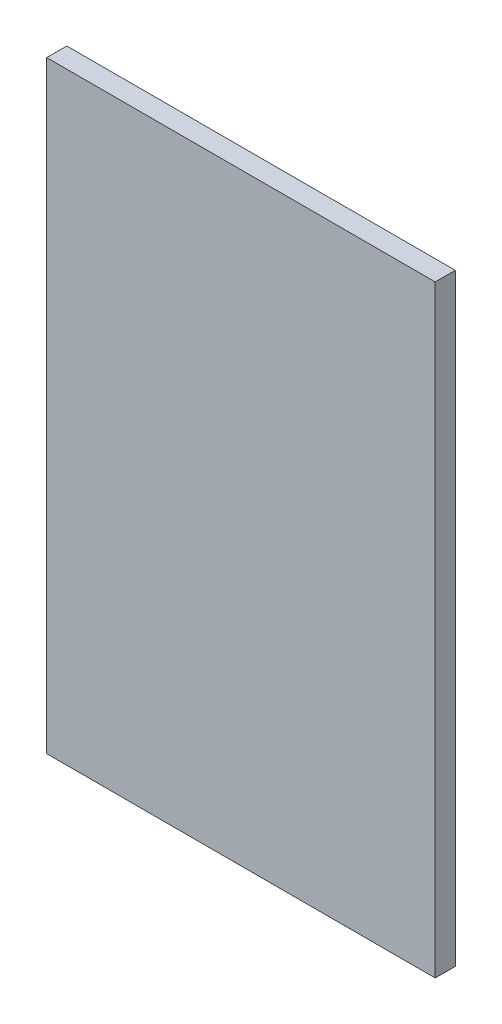
SolidWorks part; units mm, degrees
ref_plane "Plan de face" through (0, 0, 0) normal (0, 0, 1) x (1, 0, 0)
ref_plane "Plan de dessus" through (0, 0, 0) normal (0, 1, 0) x (1, 0, 0)
ref_plane "Plan de droite" through (0, 0, 0) normal (1, 0, 0) x (0, 0, -1)
sketch "Esquisse1" plane through (0, 0, 0) normal (0, 0, 1) x (1, 0, 0)
  line L1 (0, 0) -> (58, 0)
  line L2 (0, 0) -> (0, -90)
  line L3 (0, -90) -> (58, -90)
  line L4 (58, 0) -> (58, -90)
  dimension "D1" = 58
  dimension "D2" = 90
extrude "Boss.-Extru.1" add sketch "Esquisse1" along normal blind 3
